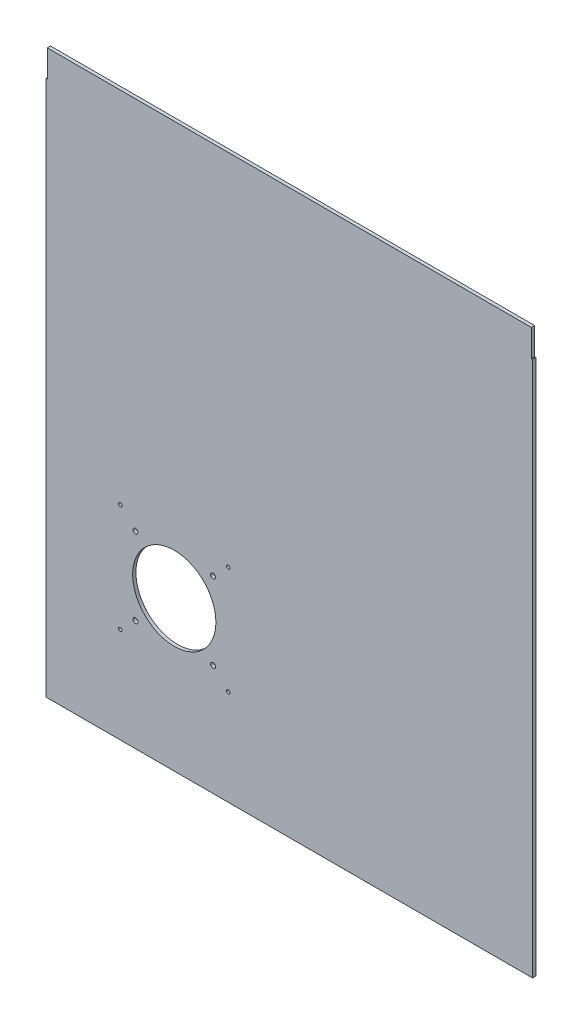
SolidWorks part; units mm, degrees
ref_plane "Alzado" through (0, 0, 0) normal (0, 0, 1) x (1, 0, 0)
ref_plane "Planta" through (0, 0, 0) normal (0, 1, 0) x (1, 0, 0)
ref_plane "Vista lateral" through (0, 0, 0) normal (1, 0, 0) x (0, 0, -1)
sketch "Croquis1" plane through (0, 0, 0) normal (0, 0, 1) x (1, 0, 0)
  line L0 (-261.8387, 298.7033) -> (-260.8387, 298.7033)
  line L1 (-260.8387, 323.7033) -> (187.1613, 323.7033)
  line L2 (-261.8387, 298.7033) -> (-261.8387, -197.0967)
  line L3 (-261.8387, -197.0967) -> (188.1613, -197.0967)
  line L4 (188.1613, 298.7033) -> (188.1613, -197.0967)
  line L5 (-260.8387, 298.7033) -> (-260.8387, 323.7033)
  line L6 (187.1613, 323.7033) -> (187.1613, 298.7033)
  line L7 (187.1613, 298.7033) -> (188.1613, 298.7033)
  dimension "D1" = 520.8
  dimension "D2" = 450
  dimension "D3" = 1
  dimension "D4" = 25
  dimension "D5" = 1
  dimension "D6" = 25
extrude "Saliente-Extruir1" add sketch "Croquis1" along normal blind 3
sketch "Croquis2" plane through (0, 0, 3) normal (0, 0, 1) x (1, 0, 0)
  line L0 (-261.8387, -197.0967) -> (188.1613, -197.0967) construction
  line L1 (-181.8387, -20.0967) -> (-104.8387, -20.0967) construction
  line L2 (-181.8387, -20.0967) -> (-181.8387, -97.0967) construction
  line L3 (-181.8387, -97.0967) -> (-104.8387, -97.0967) construction
  line L4 (-104.8387, -20.0967) -> (-104.8387, -97.0967) construction
  line L5 (-261.8387, 298.7033) -> (-261.8387, -197.0967) construction
  line L7 (-179.1887, -94.4467) -> (-107.4887, -94.4467) construction
  line L8 (-179.1887, -94.4467) -> (-179.1887, -22.7467) construction
  line L9 (-179.1887, -22.7467) -> (-107.4887, -22.7467) construction
  line L10 (-107.4887, -94.4467) -> (-107.4887, -22.7467) construction
  line L11 (-179.1887, -94.4467) -> (-107.4887, -22.7467) construction
  line L12 (-179.1887, -22.7467) -> (-107.4887, -94.4467) construction
  line L13 (-193.3387, -108.5967) -> (-93.3387, -108.5967) construction
  line L14 (-193.3387, -108.5967) -> (-193.3387, -8.5967) construction
  line L15 (-193.3387, -8.5967) -> (-93.3387, -8.5967) construction
  line L16 (-93.3387, -108.5967) -> (-93.3387, -8.5967) construction
  line L17 (-193.3387, -108.5967) -> (-93.3387, -8.5967) construction
  line L18 (-193.3387, -8.5967) -> (-93.3387, -108.5967) construction
  circle A0 centre (-143.3387, -58.5967) radius 38.5
  circle A1 centre (-107.4887, -22.7467) radius 2.25
  circle A2 centre (-107.4887, -94.4467) radius 2.25
  circle A3 centre (-179.1887, -94.4467) radius 2.25
  circle A4 centre (-179.1887, -22.7467) radius 2.25
  circle A5 centre (-93.3387, -8.5967) radius 1.6
  circle A6 centre (-93.3387, -108.5967) radius 1.6
  circle A7 centre (-193.3387, -108.5967) radius 1.6
  circle A8 centre (-193.3387, -8.5967) radius 1.6
  point P15 (-104.8387, -58.5967)
  point P17 (-143.3387, -20.0967)
  dimension "D6" = 4.5
  dimension "D9" = 3.2
  dimension "D1" = 77
  dimension "D2" = 77
  dimension "D3" = 100
  dimension "D4" = 80
  dimension "D5" = 71.7
  dimension "D8" = 100
  dimension "D7" = 4
  dimension "D10" = 4
extrude "Cortar-Extruir1" cut sketch "Croquis2" against normal up to vertex (3 mm away)
